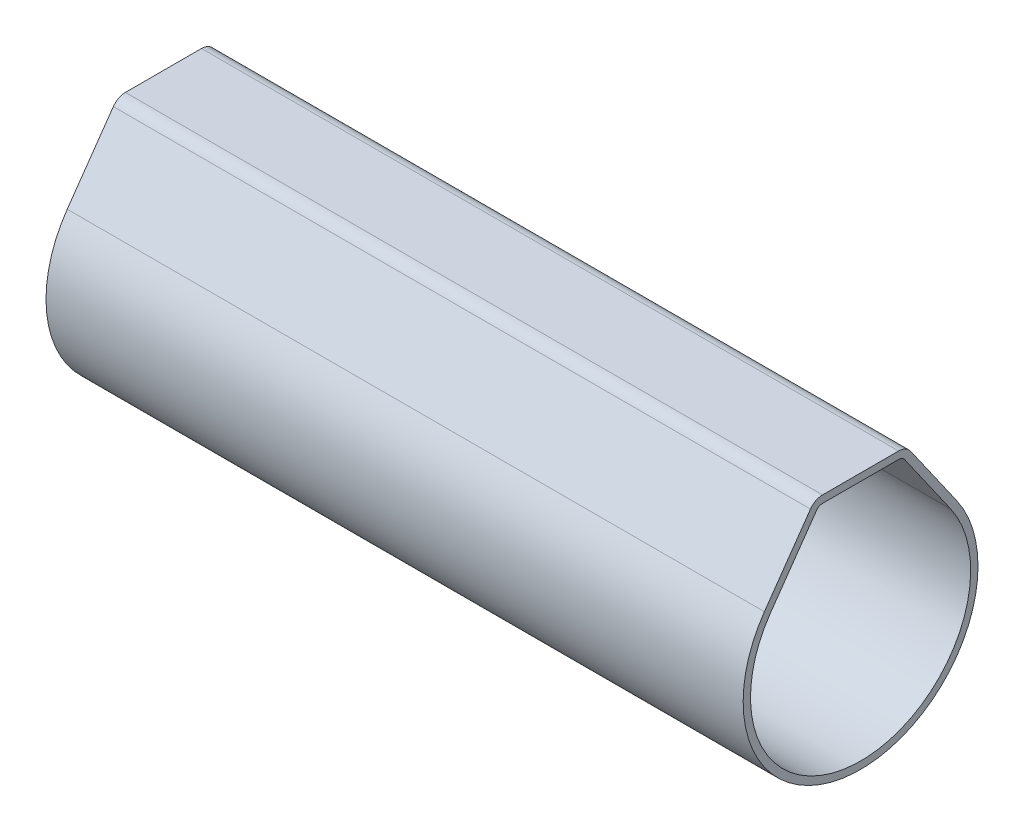
SolidWorks part; units mm, degrees
ref_plane "Ebene vorne" through (0, 0, 0) normal (0, 0, 1) x (1, 0, 0)
ref_plane "Ebene oben" through (0, 0, 0) normal (0, 1, 0) x (1, 0, 0)
ref_plane "Ebene rechts" through (0, 0, 0) normal (1, 0, 0) x (0, 0, -1)
sketch "Skizze1" plane through (0, 0, 0) normal (1, 0, 0) x (0, 0, -1)
  line L0 (-13.1064, 9.1772) -> (-6.2285, 19)
  line L1 (-6.2285, 19) -> (6.2285, 19)
  line L2 (6.2285, 19) -> (13.1064, 9.1772)
  line L3 (0, 0) -> (0, 19) construction
  arc A0 (-13.1064, 9.1772) -> (13.1064, 9.1772) centre (0, 0) ccw
  dimension "D1" = 32
  dimension "D2" = 70
  dimension "D3" = 19
extrude "Linear-Austragen-Dünn1" add sketch "Skizze1" along normal blind 95 thin
fillet "Verrundung1" radius 2 2 edges at (47.5, 19, -6.2285) (47.5, 19, 6.2285)
fillet "Verrundung2" radius 1 2 edges at (47.5, 18, 5.7079) (47.5, 18, -5.7079)
